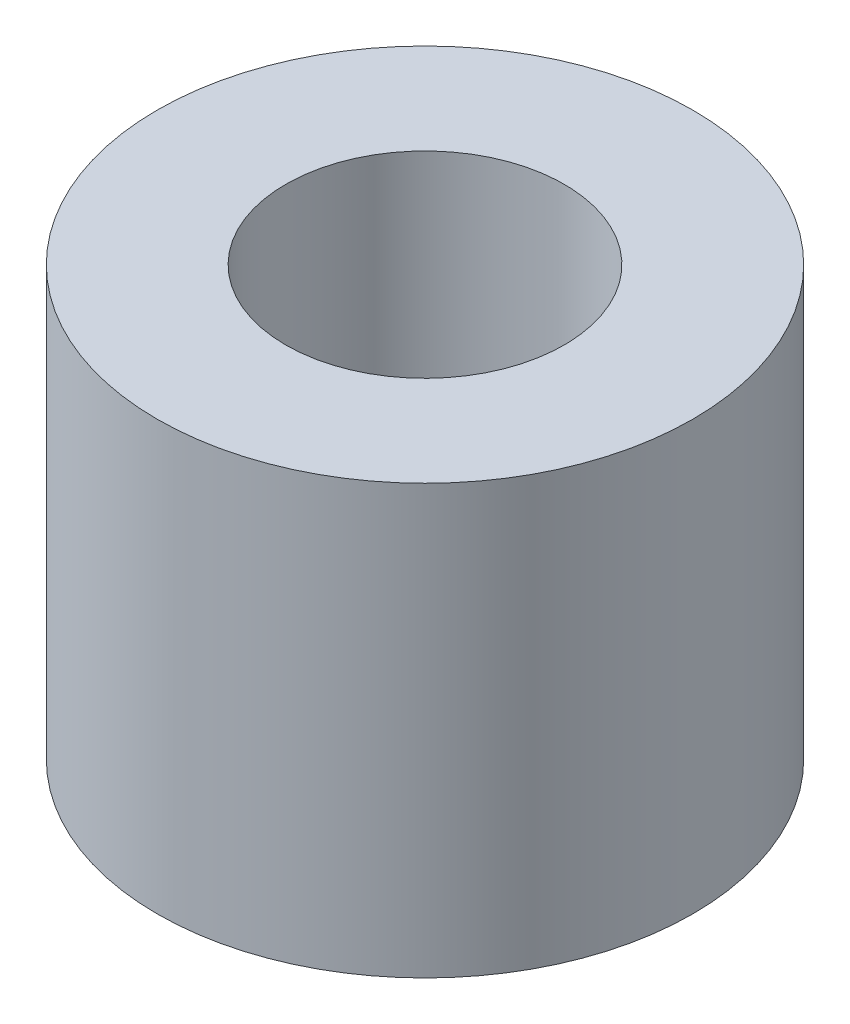
SolidWorks part; units mm, degrees
ref_plane "Front Plane" through (0, 0, 0) normal (0, 0, 1) x (1, 0, 0)
ref_plane "Top Plane" through (0, 0, 0) normal (0, 1, 0) x (1, 0, 0)
ref_plane "Right Plane" through (0, 0, 0) normal (1, 0, 0) x (0, 0, -1)
sketch "Sketch2" plane through (0, 0, 0) normal (0, 1, 0) x (1, 0, 0)
  circle A0 centre (0, 0) radius 6.35
  circle A1 centre (0, 0) radius 3.302
  dimension "D1" = 6.604
  dimension "D2" = 12.7
extrude "Boss-Extrude1" add sketch "Sketch2" along normal blind 10.16
